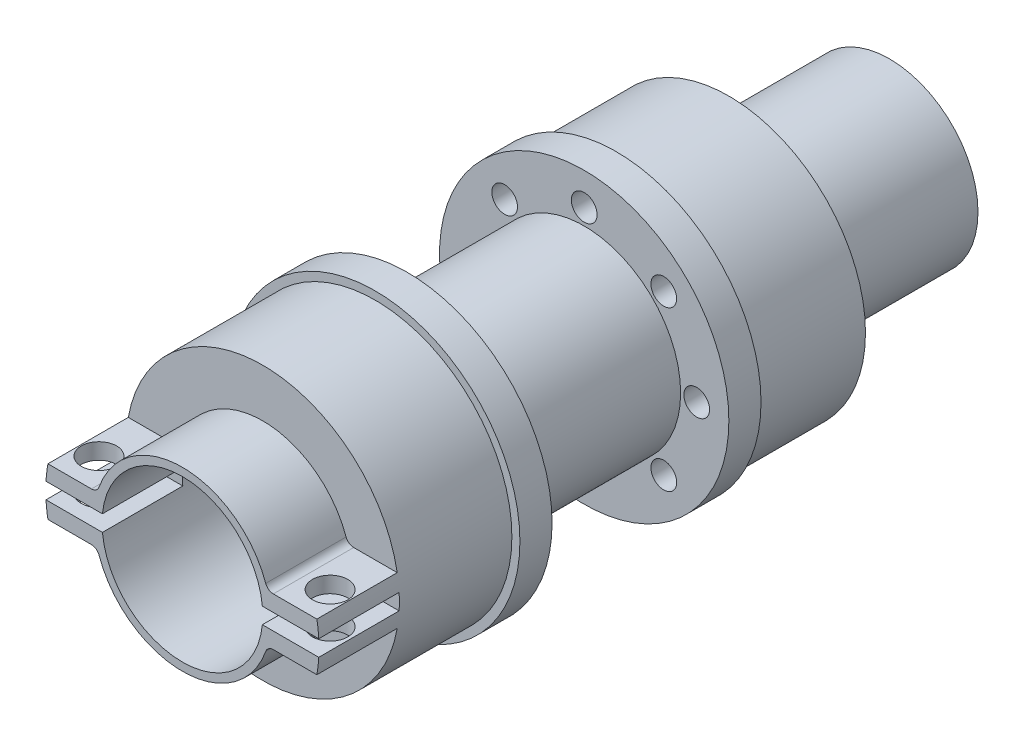
SolidWorks part; units mm, degrees
material "Alliage 1060"
ref_plane "Plan de face" through (0, 0, 0) normal (0, 0, 1) x (1, 0, 0)
ref_plane "Plan de dessus" through (0, 0, 0) normal (0, 1, 0) x (1, 0, 0)
ref_plane "Plan de droite" through (0, 0, 0) normal (1, 0, 0) x (0, 0, -1)
sketch "Esquisse1" plane through (0, 0, 0) normal (0, 0, 1) x (1, 0, 0)
  circle A0 centre (0, 0) radius 4.5
  circle A1 centre (0, 0) radius 5.5
  dimension "D1" = 9
  dimension "D2" = 11
extrude "Boss.-Extru.1" add sketch "Esquisse1" along normal blind 10
sketch "Esquisse3" plane through (0, 0, 10) normal (0, 0, 1) x (1, 0, 0)
  circle A0 centre (0, 0) radius 8.5
  circle A1 centre (0, 0) radius 5
  dimension "D1" = 10
  dimension "D2" = 17
extrude "Boss.-Extru.3" add sketch "Esquisse3" along normal blind 7
sketch "Esquisse4" plane through (0, 0, 17) normal (0, 0, 1) x (1, 0, 0)
  circle A0 centre (0, 0) radius 5
  circle A1 centre (0, 0) radius 9
  dimension "D1" = 10
  dimension "D2" = 18
extrude "Boss.-Extru.4" add sketch "Esquisse4" along normal blind 2
sketch "Esquisse7" plane through (0, 0, 19) normal (0, 0, 1) x (1, 0, 0)
  circle A0 centre (0, 0) radius 5
  circle A1 centre (0, 0) radius 6
  dimension "D1" = 10
  dimension "D2" = 12
extrude "Boss.-Extru.7" add sketch "Esquisse7" along normal blind 11
sketch "Esquisse8" plane through (0, 0, 30) normal (0, 0, 1) x (1, 0, 0)
  circle A0 centre (0, 0) radius 5
  circle A1 centre (0, 0) radius 9
  dimension "D1" = 10
  dimension "D2" = 18
extrude "Boss.-Extru.8" add sketch "Esquisse8" along normal blind 2
sketch "Esquisse15" plane through (0, 0, 32) normal (0, 0, 1) x (1, 0, 0)
  circle A0 centre (0, 0) radius 5
  circle A1 centre (0, 0) radius 8.5
  dimension "D1" = 10
  dimension "D2" = 17
extrude "Boss.-Extru.9" add sketch "Esquisse15" along normal blind 7
sketch "Esquisse16" plane through (0, 0, 39) normal (0, 0, 1) x (1, 0, 0)
  line L0 (-5.2915, 1.5) -> (-8.3666, 1.5)
  line L2 (-8.3666, -1.5) -> (-5.2915, -1.5)
  line L3 (5.2915, 1.5) -> (8.3666, 1.5)
  line L5 (8.3666, -1.5) -> (5.2915, -1.5)
  circle A0 centre (0, 0) radius 5
  arc A1 (5.2915, 1.5) -> (-5.2915, 1.5) centre (0, 0) ccw
  circle A2 centre (0, 0) radius 8.5 construction
  arc A3 (-8.3666, 1.5) -> (-8.3666, -1.5) centre (0, 0) ccw
  arc A4 (-5.2915, -1.5) -> (5.2915, -1.5) centre (0, 0) ccw
  arc A5 (8.3666, -1.5) -> (8.3666, 1.5) centre (0, 0) ccw
  dimension "D1" = 10
  dimension "D2" = 11
  dimension "D3" = 3
  dimension "D4" = 3
  dimension "D5" = 1.5
  dimension "D6" = 1.5
extrude "Boss.-Extru.10" add sketch "Esquisse16" along normal blind 5
hole_wizard "Trou pour taraudage pour trou taraudé M21" positions "Esquisse21" profile "Esquisse22" hole size "M2" standard "ISO" end condition up to next
sketch "Esquisse21" plane through (0, 0, 10) normal (0, 0, -1) x (-1, 0, 0)
  point P0 (-7, 0)
  point P11 (-4.9497, 4.9497)
  point P12 (0, 7)
  point P13 (4.9497, 4.9497)
  point P14 (7, 0)
  point P15 (4.9497, -4.9497)
  point P16 (0, -7)
  point P17 (-4.9497, -4.9497)
  point P18 (0, 0)
  dimension "D1" = 7
  dimension "D2" = 8
sketch "Esquisse22" plane through (7, 0, 10) normal (1, 0, 0) x (0, 1, 0)
  line L0 (0, 0) -> (0, 9)
  line L1 (0, 9) -> (0.8, 9)
  line L2 (0.8, 9) -> (0.8, 0)
  line L5 (0.8, 0) -> (0, 0)
  line L11 (0, -6.35) -> (0, 107.95) construction
  dimension "Diamètre du perçage jusqu'au prochain" = 1.6
  dimension "Profondeur du perçage jusqu'au prochain" = 9
sketch "Esquisse17" plane through (0, 0, 44) normal (0, 0, 1) x (1, 0, 0)
  line L1 (-10, 0.5) -> (10, 0.5)
  line L2 (-10, 0.5) -> (-10, -0.5)
  line L3 (-10, -0.5) -> (10, -0.5)
  line L4 (10, 0.5) -> (10, -0.5)
  dimension "D1" = 1
  dimension "D2" = 0.5
  dimension "D3" = 10
  dimension "D4" = 20
extrude "Enlèv. mat.-Extru.1" cut sketch "Esquisse17" against normal blind 5
hole_wizard "Dégagement M21" positions "Esquisse23" profile "Esquisse25" hole size "M2" standard "ISO"
sketch "Esquisse23" plane through (0, 1.5, 0) normal (0, 1, 0) x (1, 0, 0)
  line L1 (-5.2915, -44) -> (-5.2915, -39) construction
  line L2 (5.2915, -44) -> (5.2915, -39) construction
  line L3 (-5.2915, -44) -> (-8.3666, -44) construction
  line L4 (8.3666, -44) -> (5.2915, -44) construction
  point P0 (7.1915, -42)
  point P2 (-7.1915, -42)
  point P14 (0, 0)
  dimension "D1" = 1.9
  dimension "D2" = 1.9
  dimension "D3" = 2
  dimension "D4" = 2
sketch "Esquisse25" plane through (7.1915, 1.5, 42) normal (1, 0, 0) x (0, 0, 1)
  line L0 (0, 0) -> (0, 3.6599)
  line L1 (0, 3.6599) -> (1.1, 2.999)
  line L2 (1.1, 2.999) -> (1.1, 0)
  line L5 (1.1, 0) -> (0, 0)
  line L10 (0, 3.6599) -> (-1.1, 2.999) construction
  line L11 (0, -6.35) -> (0, 107.95) construction
  dimension "Diamètre du perçage" = 2.2
  dimension "Profondeur du perçage" = 2.999
  dimension "Angle de pointe" = 118
fillet "Congé1" radius 0.5 4 edges at (-5.2915, -1.5, 41.5) (5.2915, -1.5, 41.5) (5.2915, 1.5, 41.5) (-5.2915, 1.5, 41.5)
